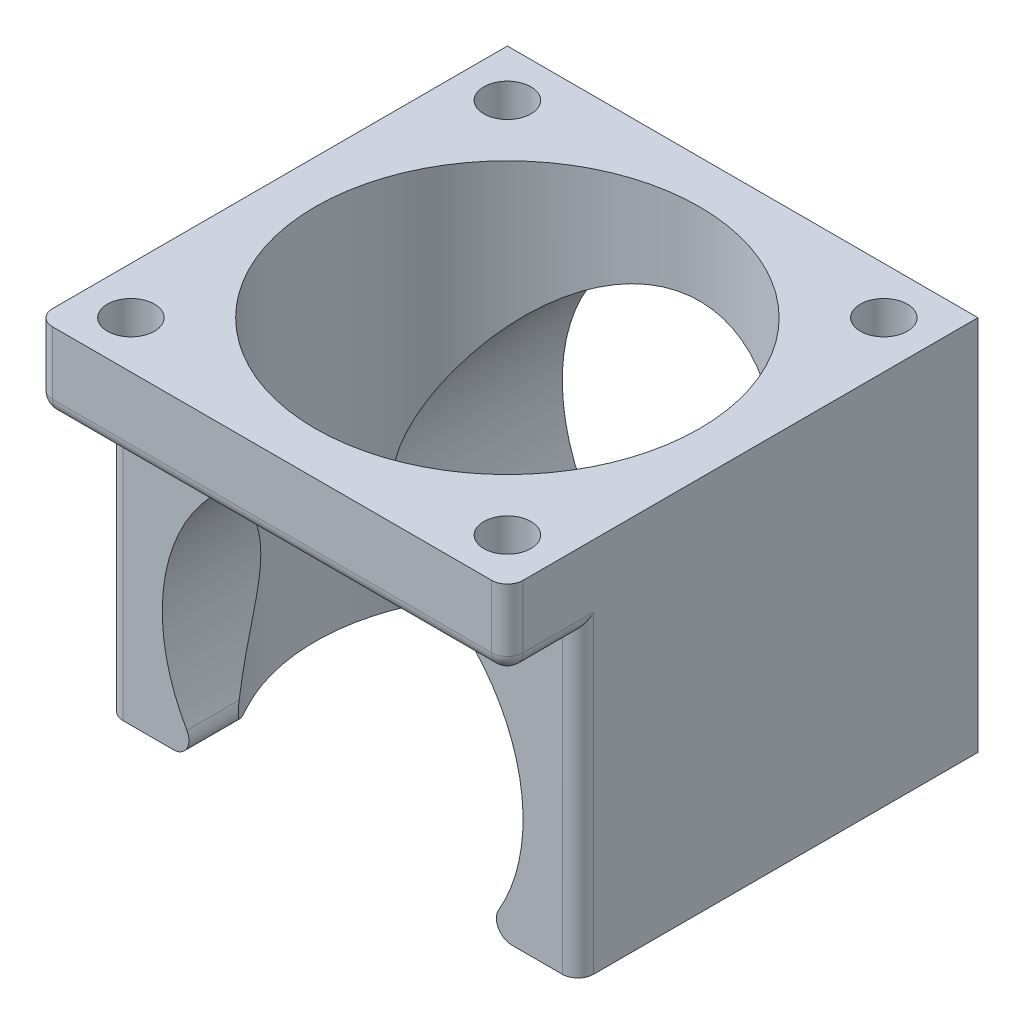
SolidWorks part; units mm, degrees
ref_plane "Front Plane" through (0, 0, 0) normal (0, 0, 1) x (1, 0, 0)
ref_plane "Top Plane" through (0, 0, 0) normal (0, 1, 0) x (1, 0, 0)
ref_plane "Right Plane" through (0, 0, 0) normal (1, 0, 0) x (0, 0, -1)
sketch "Sketch1" plane through (0, 0, 0) normal (0, 1, 0) x (1, 0, 0)
  line L0 (-18.6486, -5.3378) -> (13.718, -5.3378)
  line L1 (-18.6486, 9.6622) -> (11.3514, 9.6622)
  line L2 (-18.6486, 9.6622) -> (-18.6486, -20.3378)
  line L3 (-18.6486, -20.3378) -> (11.3514, -20.3378)
  line L4 (11.3514, 9.6622) -> (11.3514, -20.3378)
  line L5 (-3.6486, 9.6622) -> (-3.6486, -20.3378)
  circle A0 centre (-15.6486, 6.6622) radius 1.5
  circle A1 centre (8.3514, 6.6622) radius 1.5
  circle A2 centre (8.3514, -17.3378) radius 1.5
  circle A3 centre (-15.6486, -17.3378) radius 1.5
  circle A4 centre (-3.6486, -5.3378) radius 12.25
  dimension "D1" = 30
  dimension "D2" = 30
  dimension "D3" = 3
  dimension "D4" = 3
extrude "Boss-Extrude1" add sketch "Sketch1" along normal blind 5 contours A4 L0 L2 L3 L5 A3 | A4 L5 L3 L4 L0 A2 | A4 L0 L4 L1 L5 A1 | A4 L5 L1 L2 L0 A0
sketch "Sketch3" plane through (0, 0, 0) normal (0, -1, 0) x (1, 0, 0)
  line L0 (-18.6486, -9.6622) -> (-18.6486, 20.3378) construction
  line L1 (11.3514, -9.6622) -> (-18.6486, -9.6622)
  line L2 (11.3514, -9.6622) -> (11.3514, 15.8378)
  line L3 (11.3514, 15.8378) -> (-18.6486, 15.8378)
  line L4 (-18.6486, -9.6622) -> (-18.6486, 15.8378)
  dimension "D1" = 25.5
extrude "Boss-Extrude2" add sketch "Sketch3" along normal blind 19
sketch "Sketch4" plane through (0, 0, 15.8378) normal (0, 0, 1) x (1, 0, 0)
  line L0 (-3.6486, 0) -> (-3.6486, -23.4)
  line L1 (-18.6486, 0) -> (11.3514, 0) construction
  circle A0 centre (-3.6486, -11.7) radius 11.5
  line M7 (-18.6486, -19) -> (11.3514, -19)
  dimension "D1" = 23
extrude "Cut-Extrude7" cut sketch "Sketch4" against normal through all contours L0 A0 M7 | A0 L0 M7
sketch "Sketch5" plane through (0, 0, 0) normal (0, 1, 0) x (1, 0, 0)
  circle A0 centre (-3.6486, -5.3378) radius 12.25
  circle A1 centre (-3.6486, -5.3378) radius 12.25
  line M2 (-9.9584, -15.8378) -> (2.6611, -15.8378)
  arc M3 (2.6611, -15.8378) -> (-9.9584, -15.8378) centre (-3.6486, -5.3378) ccw
fillet "Fillet10" radius 1 7 edges at (11.3514, 2.5, 20.3378) (-18.6486, 2.5, 20.3378) (-3.6486, 0, 20.3378)
fillet "Fillet11" radius 1 2 edges at (-12.5346, -19, 3.0878) (5.2373, -19, 3.0878)
extrude "Cut-Extrude9" cut sketch "Sketch5" against normal through all contours M3 M2
